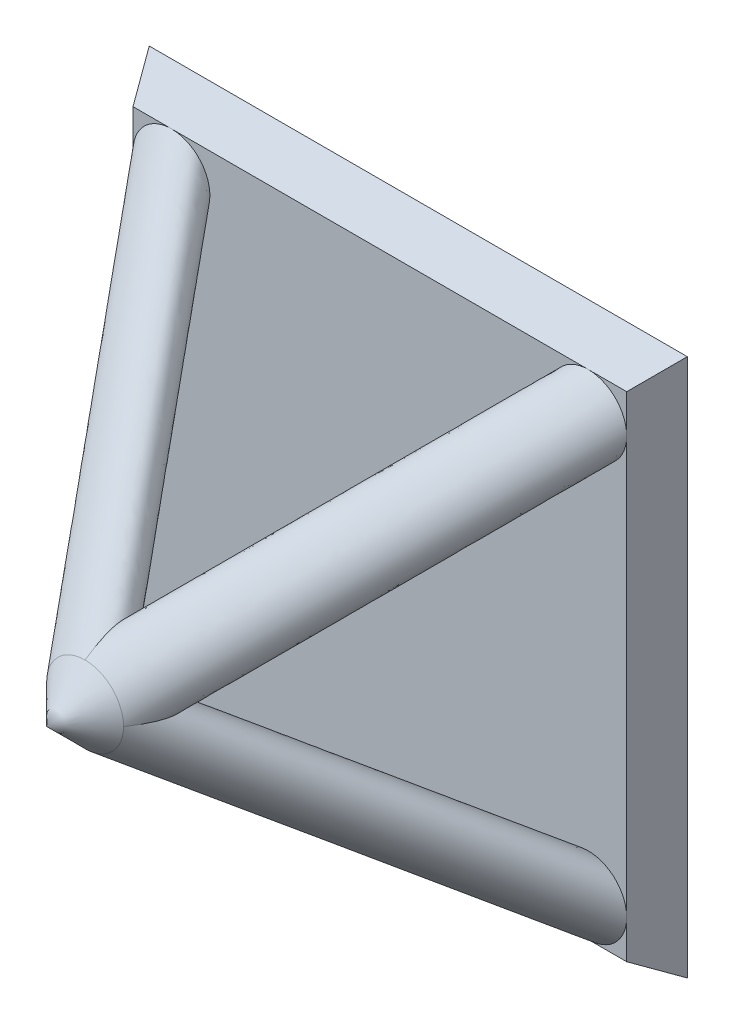
SolidWorks part; units mm, degrees
ref_plane "Front" through (0, 0, 0) normal (0, 0, 1) x (1, 0, 0)
ref_plane "Top" through (0, 0, 0) normal (0, 1, 0) x (1, 0, 0)
ref_plane "Right" through (0, 0, 0) normal (1, 0, 0) x (0, 0, -1)
sketch "Sketch1" plane through (0, 0, 0) normal (0, 0, 1) x (1, 0, 0)
  line L0 (0, 0) -> (0, 43.0475) construction
  line L1 (-7, 7) -> (7, 7)
  line L2 (-7, 7) -> (-7, -7)
  line L3 (-7, -7) -> (7, -7)
  line L4 (7, 7) -> (7, -7)
  line L5 (0, 0) -> (74.4916, 0) construction
  point P7 (0, 7)
  point P8 (7, 0)
  dimension "D1" = 14
  dimension "D2" = 14
extrude "Boss-Extrude1" add sketch "Sketch1" along normal blind 1 draft 30
sketch "Sketch2" plane through (0, 0, 1) normal (0, 0, 1) x (1, 0, 0)
  line L0 (6.4226, -6.4226) -> (6.4226, 6.4226) construction
  line L1 (6.4226, 6.4226) -> (-6.4226, 6.4226) construction
  circle A0 centre (5.4226, 5.4226) radius 1
  dimension "D1" = 2
ref_plane "Plane1" through (0, 0, 0) normal (0.7071, -0.7071, 0) x (0, 0, -1)
sketch "Sketch3" plane through (0, 0, 0) normal (0.7071, -0.7071, 0) x (0, 0, -1)
  line L0 (-1, 7.6688) -> (-8.6688, 0)
  line L1 (0, 0) -> (-12.2099, 0) construction
sweep "Sweep1" add profiles "Sketch2" path "Sketch3"
ref_axis "Axis1" through (0, 0, -4.2318) along (0, 0, 1)
pattern_circular "CirPattern1" count 4 over 360 about axis through (0, 0, -4.2318) along (0, 0, 1) of "Sweep1"
sketch "Sketch4" plane through (0, 0, 8.6688) normal (0, 0, 1) x (1, 0, 0)
  circle A0 centre (0, 0) radius 1
extrude "Boss-Extrude2" add sketch "Sketch4" along normal blind 10 draft 45
scale "Scale1" bodies to scale 106 scale about centroid uniform scaling yes scale factor 0.5
